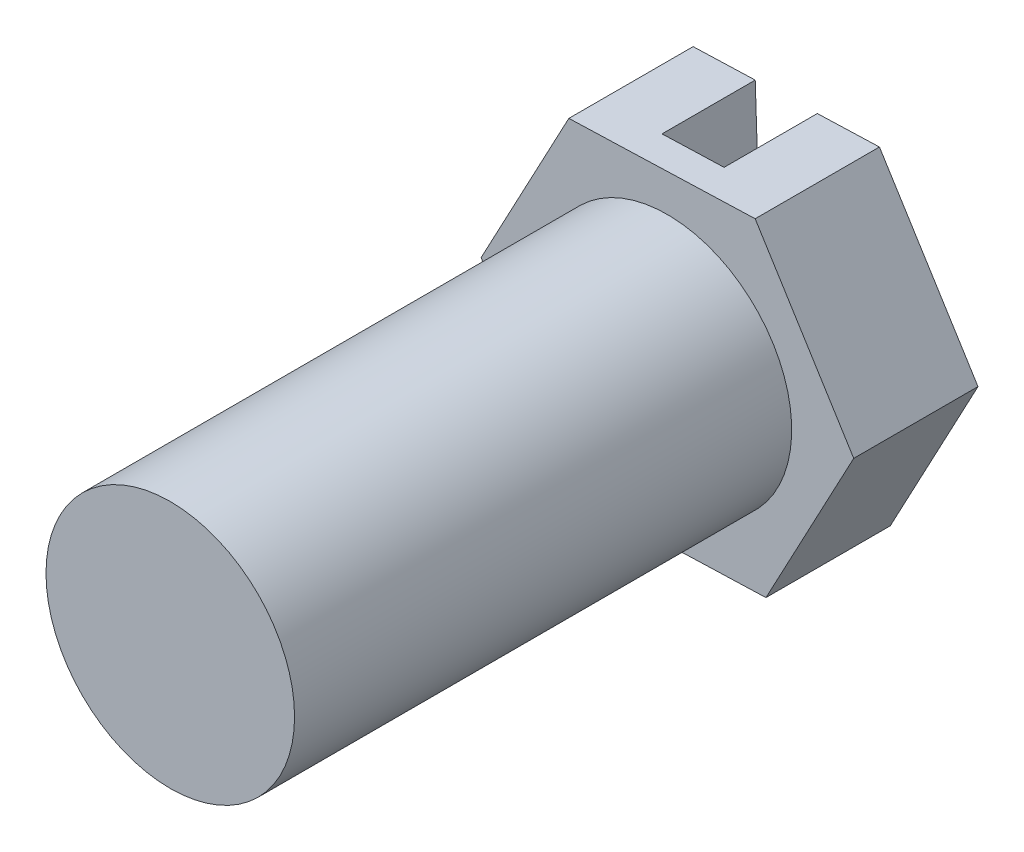
SolidWorks part; units mm, degrees
ref_plane "前视基准面" through (0, 0, 0) normal (0, 0, 1) x (1, 0, 0)
ref_plane "上视基准面" through (0, 0, 0) normal (0, 1, 0) x (1, 0, 0)
ref_plane "右视基准面" through (0, 0, 0) normal (1, 0, 0) x (0, 0, -1)
sketch "草图1" plane through (0, 0, 0) normal (0, 0, 1) x (1, 0, 0)
  circle A0 centre (0, 0) radius 0.2
  dimension "D1" = 0.4
extrude "凸台-拉伸1" add sketch "草图1" along normal blind 0.8
sketch "草图2" plane through (0, 0, 0) normal (0, 0, -1) x (-1, 0, 0)
  circle A0 centre (0, 0) radius 0.3
extrude "凸台-拉伸2" add sketch "草图2" along normal blind 0.2
sketch "草图3" plane through (0, 0, -0.2) normal (0, 0, -1) x (-1, 0, 0)
  line L1 (0.1412, -0.2647) -> (0.2998, -0.01)
  line L2 (0.2998, -0.01) -> (0.1586, 0.2546)
  line L3 (0.1586, 0.2546) -> (-0.1412, 0.2647)
  line L4 (-0.1412, 0.2647) -> (-0.2998, 0.01)
  line L5 (-0.2998, 0.01) -> (-0.1586, -0.2546)
  line L6 (-0.1586, -0.2546) -> (0.1412, -0.2647)
  circle A0 centre (0, 0) radius 0.2598 construction
  circle A1 centre (0, 0) radius 0.3403
extrude "切除-拉伸1" cut sketch "草图3" against normal blind 0.2
sketch "草图4" plane through (0, 0, -0.2) normal (0, 0, -1) x (-1, 0, 0)
  line L0 (-0.0087, -0.2597) -> (0.0087, 0.2597)
  line L1 (-0.1586, -0.2546) -> (0.1412, -0.2647) construction
  line L2 (0.1586, 0.2546) -> (-0.1412, 0.2647) construction
  line L3 (0.0413, -0.2613) -> (0.0587, 0.258)
  line L4 (-0.0587, -0.258) -> (-0.0413, 0.2613)
  line L5 (0.0413, -0.2613) -> (-0.0587, -0.258)
  line L6 (-0.0413, 0.2613) -> (0.0587, 0.258)
  dimension "D1" = 0.05
  dimension "D2" = 0.05
extrude "切除-拉伸2" cut sketch "草图4" against normal blind 0.15 contours L4 L6 L3 L5
